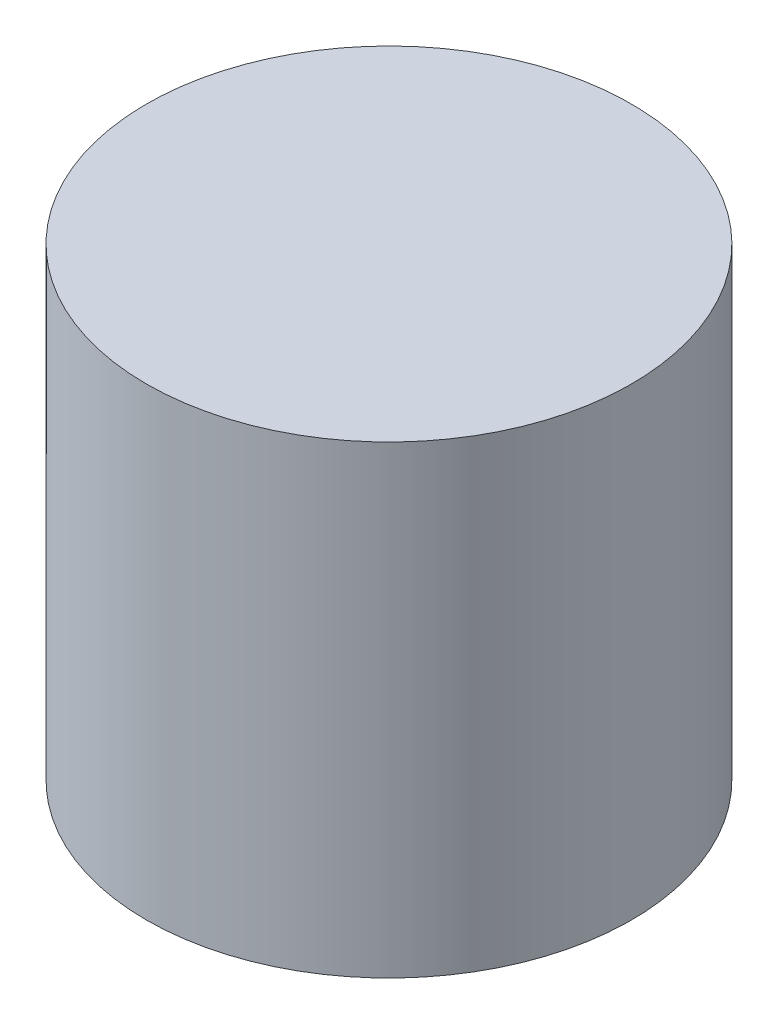
SolidWorks part; units mm, degrees
ref_plane "Front Plane" through (0, 0, 0) normal (0, 0, 1) x (1, 0, 0)
ref_plane "Top Plane" through (0, 0, 0) normal (0, 1, 0) x (1, 0, 0)
ref_plane "Right Plane" through (0, 0, 0) normal (1, 0, 0) x (0, 0, -1)
sketch "Sketch1" plane through (0, 0, 0) normal (0, 1, 0) x (1, 0, 0)
  circle A0 centre (0, 0) radius 44.45
  dimension "D1" = 88.9
extrude "Extrude1" add sketch "Sketch1" along normal blind 85.09
